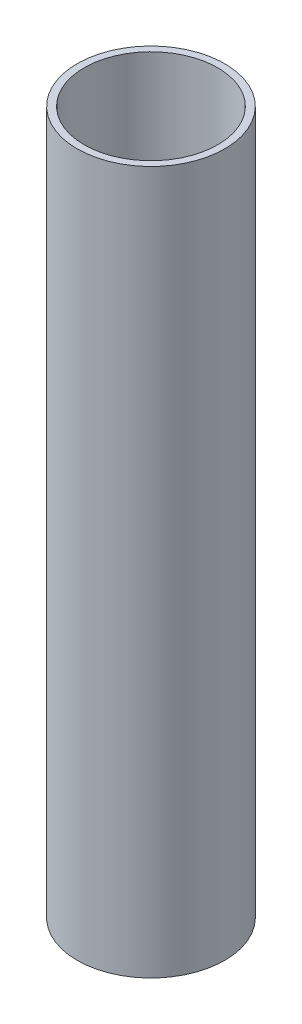
SolidWorks part; units mm, degrees
ref_plane "Front Plane" through (0, 0, 0) normal (0, 0, 1) x (1, 0, 0)
ref_plane "Top Plane" through (0, 0, 0) normal (0, 1, 0) x (1, 0, 0)
ref_plane "Right Plane" through (0, 0, 0) normal (1, 0, 0) x (0, 0, -1)
sketch "Sketch1" plane through (0, 0, 0) normal (0, 1, 0) x (1, 0, 0)
  circle A0 centre (0, 0) radius 10.5
  circle A1 centre (0, 0) radius 9.5
  dimension "D1" = 21
  dimension "D2" = 1
extrude "Boss-Extrude1" add sketch "Sketch1" along normal blind 100
